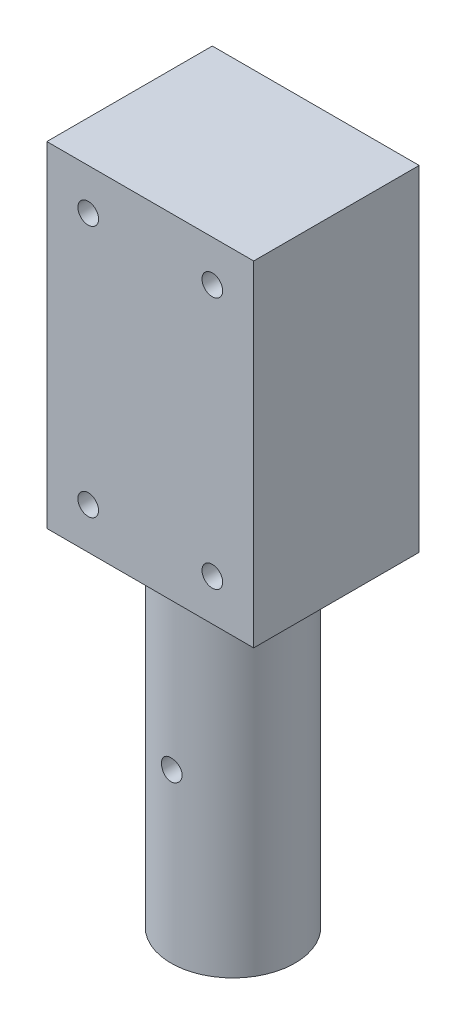
SolidWorks part; units mm, degrees
material "3003 Alloy"
ref_plane "Front Plane" through (0, 0, 0) normal (0, 0, 1) x (1, 0, 0)
ref_plane "Top Plane" through (0, 0, 0) normal (0, 1, 0) x (1, 0, 0)
ref_plane "Right Plane" through (0, 0, 0) normal (1, 0, 0) x (0, 0, -1)
other "Center of Mass"
sketch "Sketch1" plane through (0, 0, 0) normal (0, 1, 0) x (1, 0, 0)
  line L1 (0, 0) -> (50, 0)
  line L2 (0, 0) -> (0, 40)
  line L3 (0, 40) -> (50, 40)
  line L4 (50, 0) -> (50, 40)
  dimension "D1" = 50
  dimension "D2" = 40
extrude "Boss-Extrude1" add sketch "Sketch1" along normal blind 81
sketch "Sketch2" plane through (0, 0, 0) normal (0, -1, 0) x (1, 0, 0)
  line L0 (25, 0) -> (25, -40) construction
  line L1 (0, 0) -> (50, 0) construction
  line L2 (50, -40) -> (0, -40) construction
  circle A0 centre (25, -20) radius 15
  dimension "D1" = 30
extrude "Boss-Extrude2" add sketch "Sketch2" along normal blind 81
sketch "Sketch3" plane through (0, 0, 0) normal (0, 0, 1) x (1, 0, 0)
  line L0 (0, 0) -> (50, 0) construction
  line L1 (0, 81) -> (0, 0) construction
  circle A0 centre (25, -40.5) radius 2.5
  point P2 (25, -14.9154)
  dimension "D2" = 5
  dimension "D3" = 25
  dimension "D1" = 40.5
extrude "Cut-Extrude1" cut sketch "Sketch3" against normal through all
sketch "Sketch4" plane through (0, 0, 0) normal (0, 0, 1) x (1, 0, 0)
  line L0 (0, 81) -> (50, 81) construction
  line L1 (0, 81) -> (0, 0) construction
  line L2 (50, 81) -> (50, 0) construction
  line L3 (0, 0) -> (50, 0) construction
  circle A0 centre (10, 71) radius 3
  circle A1 centre (40, 71) radius 3
  circle A2 centre (40, 10) radius 3
  circle A3 centre (10, 10) radius 3
  point P8 (0, 0)
  point P9 (0, 0)
  point P10 (0, 0)
  point P11 (0, 0)
  dimension "D1" = 6
  dimension "D2" = 6
  dimension "D3" = 6
  dimension "D4" = 6
  dimension "D5" = 10
  dimension "D6" = 10
  dimension "D7" = 10
  dimension "D8" = 10
hole_wizard "M6 Tapped Hole1" positions "Sketch5" profile "Sketch6" tap size "M6" standard "ISO"
sketch "Sketch5" plane through (0, 0, 0) normal (0, 0, 1) x (1, 0, 0)
  point P0 (10, 10)
  point P3 (40, 10)
  point P6 (40, 71)
  point P9 (10, 71)
sketch "Sketch6" plane through (10, 10, 0) normal (1, 0, 0) x (0, -1, 0)
  line L0 (0, 0) -> (0, 15)
  line L1 (0, 15) -> (2.5, 13.4978)
  line L2 (2.5, 13.4978) -> (2.5, 0)
  line L5 (2.5, 0) -> (0, 0)
  line L10 (0, 15) -> (-2.5, 13.4978) construction
  line L11 (0, -6.35) -> (0, 107.95) construction
  dimension "Tap Drill Dia." = 5
  dimension "Tap Drill Depth" = 15
  dimension "Drill Angle" = 118
cosmetic thread "Hole Thread1" parameters "D1"=12, "D2"=6
cosmetic thread "Hole Thread2" parameters "D1"=12, "D2"=6
cosmetic thread "Hole Thread3" parameters "D1"=12, "D2"=6
cosmetic thread "Hole Thread4" parameters "D1"=12, "D2"=6
hole_wizard "M6 Tapped Hole4" positions "Sketch16" profile "Sketch18" tap size "M6" standard "ISO"
sketch "Sketch16" plane through (50.277, 10.6278, -40) normal (0, 0, -1) x (-1, 0, 0)
  line L0 (0.277, -10.6278) -> (50.277, -10.6278) construction
  line L1 (50.277, 70.3722) -> (50.277, -10.6278) construction
  line L2 (0.277, 70.3722) -> (0.277, -10.6278) construction
  line L3 (0.277, 70.3722) -> (50.277, 70.3722) construction
  point P0 (10.277, -0.6278)
  point P3 (40.277, -0.6278)
  point P6 (40.277, 60.3722)
  point P9 (10.277, 60.3722)
  point P18 (10.277, 60.3722)
  point P20 (10.277, 55.1714)
  point P21 (40.277, 55.1714)
  point P22 (0, 0)
  dimension "D1" = 10
  dimension "D2" = 10
  dimension "D3" = 10
  dimension "D4" = 10
  dimension "D5" = 10
  dimension "D6" = 10
  dimension "D7" = 10
  dimension "D8" = 10
sketch "Sketch18" plane through (40, 10, -40) normal (1, 0, 0) x (0, 1, 0)
  line L0 (0, 0) -> (0, 15)
  line L1 (0, 15) -> (2.5, 13.4978)
  line L2 (2.5, 13.4978) -> (2.5, 0)
  line L5 (2.5, 0) -> (0, 0)
  line L10 (0, 15) -> (-2.5, 13.4978) construction
  line L11 (0, -6.35) -> (0, 107.95) construction
  dimension "Tap Drill Dia." = 5
  dimension "Tap Drill Depth" = 15
  dimension "Drill Angle" = 118
cosmetic thread "Hole Thread13" parameters "D1"=12, "D2"=6
cosmetic thread "Hole Thread14" parameters "D1"=12, "D2"=6
cosmetic thread "Hole Thread15" parameters "D1"=12, "D2"=6
cosmetic thread "Hole Thread16" parameters "D1"=12, "D2"=6
